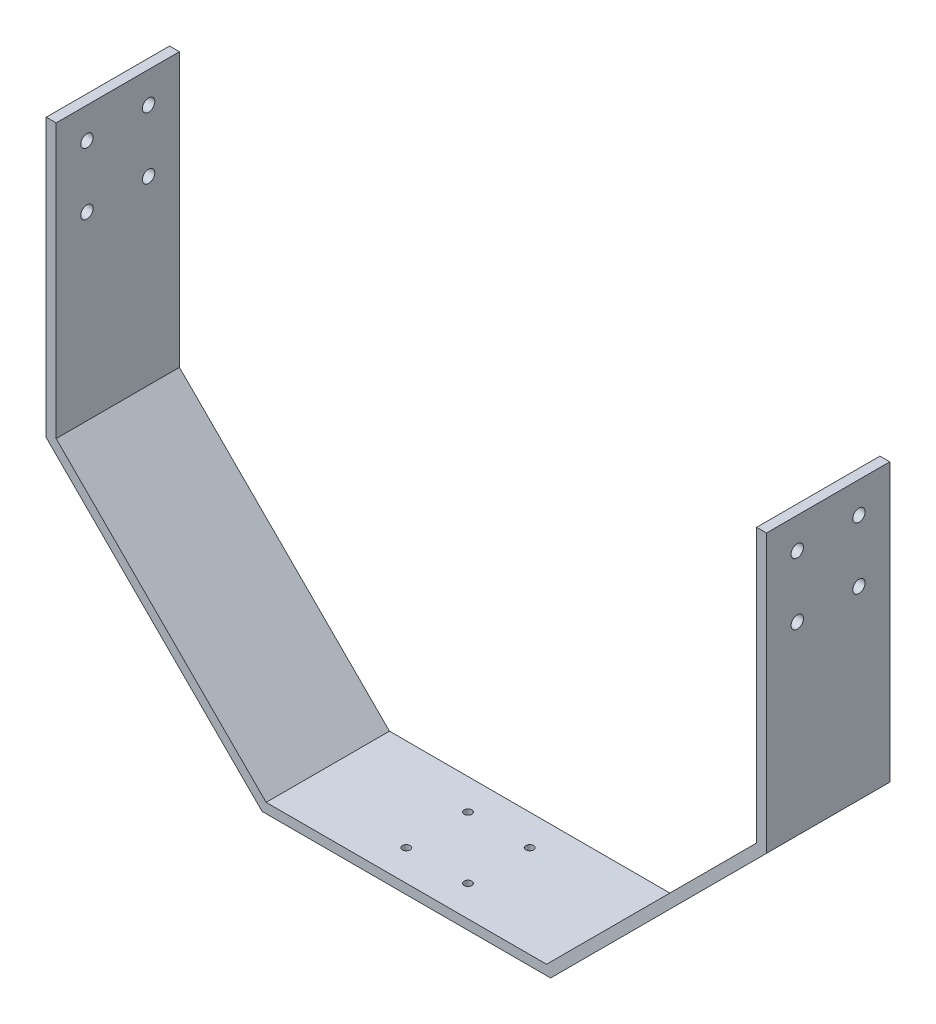
SolidWorks part; units mm, degrees
material "6061-T6 (SS)"
ref_plane "Front Plane" through (0, 0, 0) normal (0, 0, 1) x (1, 0, 0)
ref_plane "Top Plane" through (0, 0, 0) normal (0, 1, 0) x (1, 0, 0)
ref_plane "Right Plane" through (0, 0, 0) normal (1, 0, 0) x (0, 0, -1)
sketch "Sketch1" plane through (0, 0, 0) normal (0, 0, 1) x (1, 0, 0)
  line L0 (0, 203.2) -> (0, 88.9)
  line L1 (0, 0) -> (296.672, 0) construction
  line L2 (0, 0) -> (0, 203.2) construction
  line L3 (0, 203.2) -> (296.672, 203.2) construction
  line L4 (296.672, 0) -> (296.672, 203.2) construction
  line L5 (0, 88.9) -> (88.9, 0)
  line L6 (88.9, 0) -> (207.772, 0)
  line L7 (148.336, 0) -> (148.336, 203.2) construction
  line L8 (296.672, 88.9) -> (207.772, 0)
  line L9 (296.672, 203.2) -> (296.672, 88.9)
  line L10 (4.064, 203.2) -> (4.064, 90.5834)
  line L11 (4.064, 90.5834) -> (90.5834, 4.064)
  line L12 (90.5834, 4.064) -> (206.0886, 4.064)
  line L13 (292.608, 90.5834) -> (206.0886, 4.064)
  line L14 (292.608, 203.2) -> (292.608, 90.5834)
  line L15 (292.608, 203.2) -> (296.672, 203.2)
  line L16 (4.064, 203.2) -> (0, 203.2)
  circle A0 centre (148.336, 131.064) radius 127 construction
  dimension "D4" = 254
  dimension "D1" = 296.672
  dimension "D2" = 203.2
  dimension "D3" = 114.3
  dimension "D5" = 135
  dimension "D6" = 4.064
extrude "Boss-Extrude2" add sketch "Sketch1" along normal blind 50.8
hole_wizard "#10 Clearance Hole1" positions "Sketch13" profile "Sketch12" hole size "#10" standard "ANSI Inch"
sketch "Sketch13" plane through (4.064, 0, 0) normal (1, 0, 0) x (0, 0, -1)
  line L1 (-38.1, 190.5) -> (-12.7, 190.5) construction
  line L2 (-38.1, 190.5) -> (-38.1, 165.1) construction
  line L3 (-38.1, 165.1) -> (-12.7, 165.1) construction
  line L4 (-12.7, 190.5) -> (-12.7, 165.1) construction
  line L8 (-50.8, 90.5834) -> (-50.8, 203.2) construction
  line L9 (-50.8, 190.5) -> (-38.1, 190.5) construction
  line L14 (0, 90.5834) -> (0, 203.2) construction
  line L15 (0, 165.1) -> (-12.7, 165.1) construction
  line L16 (-50.8, 152.4) -> (0, 152.4) construction
  line L18 (-50.8, 203.2) -> (0, 203.2) construction
  line L19 (-25.4, 152.4) -> (-25.4, 165.1) construction
  line L21 (-25.4, 190.5) -> (-25.4, 203.2) construction
  point P1 (-38.1, 190.5)
  point P2 (-12.7, 165.1)
  point P67 (-38.1, 165.1)
  point P68 (-12.7, 190.5)
  dimension "D1" = 25.4
  dimension "D2" = 25.4
  dimension "D3" = 50.8
sketch "Sketch12" plane through (4.064, 190.5, 38.1) normal (0, 1, 0) x (0, 0, -1)
  line L0 (0, 0) -> (0, 4.064)
  line L1 (0, 4.064) -> (2.5527, 4.064)
  line L2 (2.5527, 4.064) -> (2.5527, 0)
  line L5 (2.5527, 0) -> (0, 0)
  line L11 (0, -6.35) -> (0, 107.95) construction
  dimension "Thru Hole Dia." = 5.1054
  dimension "Thru Hole Depth" = 4.064
ref_plane "Plane2" through (148.336, 0, 0) normal (1, 0, 0) x (0, 0, -1)
mirror "Mirror1" about plane through (148.336, 0, 0) normal (1, 0, 0) of "#10 Clearance Hole1"
hole_wizard "1/8 (0.125) Diameter Hole1" positions "Sketch15" profile "Sketch14" hole size "1/8" standard "ANSI Inch" end condition through all
sketch "Sketch15" plane through (0, 4.064, 0) normal (0, 1, 0) x (1, 0, 0)
  line L1 (135.636, -38.1) -> (161.036, -38.1) construction
  line L2 (135.636, -38.1) -> (135.636, -12.7) construction
  line L3 (135.636, -12.7) -> (161.036, -12.7) construction
  line L4 (161.036, -38.1) -> (161.036, -12.7) construction
  line L5 (148.336, -12.7) -> (148.336, 0) construction
  line L6 (206.0886, 0) -> (90.5834, 0) construction
  point P1 (135.636, -38.1)
  point P2 (161.036, -12.7)
  point P33 (135.636, -12.7)
  point P34 (161.036, -38.1)
  dimension "D1" = 25.4
  dimension "D2" = 25.4
  dimension "D3" = 12.7
sketch "Sketch14" plane through (135.636, 4.064, 38.1) normal (1, 0, 0) x (0, 0, 1)
  line L0 (0, 0) -> (0, 4.064)
  line L1 (0, 4.064) -> (1.5875, 4.064)
  line L2 (1.5875, 4.064) -> (1.5875, 0)
  line L5 (1.5875, 0) -> (0, 0)
  line L11 (0, -6.35) -> (0, 107.95) construction
  dimension "Thru Hole Dia." = 3.175
  dimension "Thru Hole Depth" = 4.064
